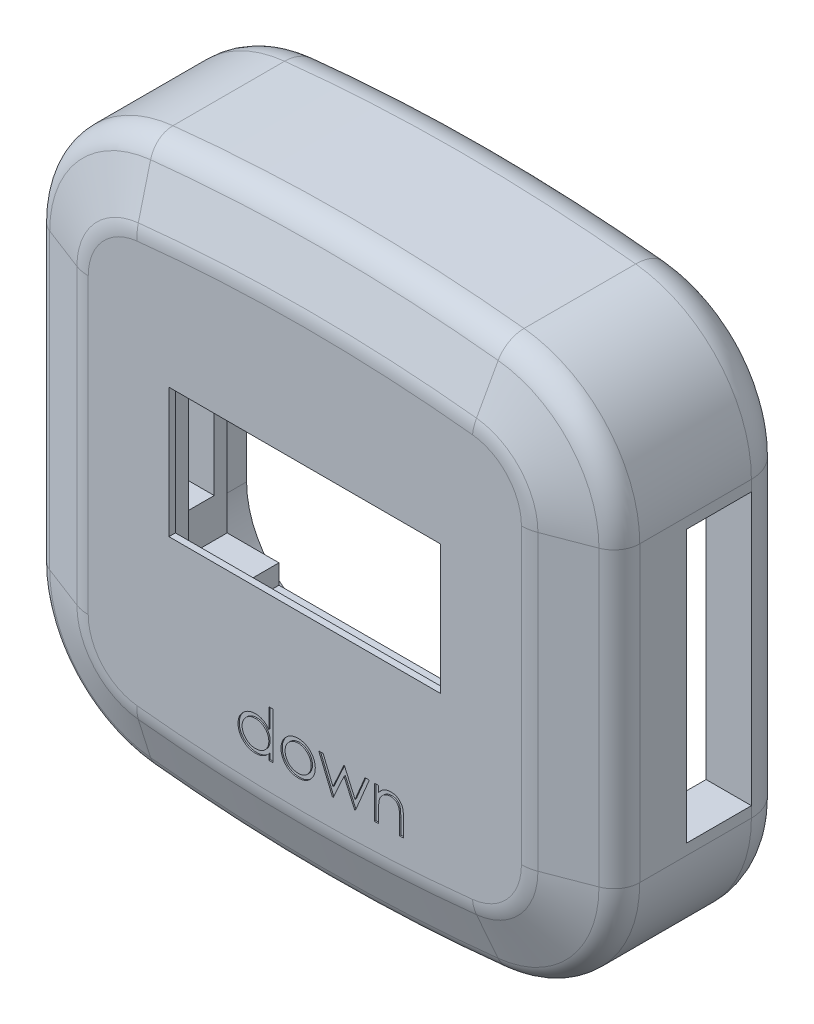
SolidWorks part; units mm, degrees
ref_plane "Plan de face" through (0, 0, 0) normal (0, 0, 1) x (1, 0, 0)
ref_plane "Plan de dessus" through (0, 0, 0) normal (0, 1, 0) x (1, 0, 0)
ref_plane "Plan de droite" through (0, 0, 0) normal (1, 0, 0) x (0, 0, -1)
sketch "Esquisse1" plane through (0, 0, 0) normal (0, 0, 1) x (1, 0, 0)
  line L0 (-2.8778, 47.4702) -> (-2.8778, -48.3378) construction
  line L1 (-25.3778, -11.7674) -> (-2.8778, -11.7674) construction
  line L2 (-25.3778, 10.8998) -> (-25.3778, -11.7674)
  line L3 (-2.8778, -11.7674) -> (19.6222, -11.7674) construction
  line L4 (19.6222, 10.8998) -> (19.6222, -11.7674)
  line L5 (40.0964, -0.4338) -> (-45.852, -0.4338) construction
  line L6 (-16.4411, 20.8431) -> (-16.4411, -0.4338) construction
  line L7 (-16.4411, -0.4338) -> (-16.4411, -21.7107) construction
  arc A0 (10.6854, 20.8431) -> (-16.4411, 20.8431) centre (-2.8778, -105.9963) ccw
  arc A1 (-16.4411, -21.7107) -> (10.6854, -21.7107) centre (-2.8778, 105.1287) ccw
  arc A3 (-16.4411, 20.8431) -> (-25.3778, 10.8998) centre (-15.3778, 10.8998) ccw
  arc A4 (-25.3778, -11.7674) -> (-16.4411, -21.7107) centre (-15.3778, -11.7674) ccw
  arc A5 (10.6854, -21.7107) -> (19.6222, -11.7674) centre (9.6222, -11.7674) ccw
  arc A7 (19.6222, 10.8998) -> (10.6854, 20.8431) centre (9.6222, 10.8998) ccw
  point P5 (-2.8778, -0.4338)
  point P7 (-2.8778, -0.4338)
  point P14 (-2.8778, -22.4338)
  point P17 (-2.8778, 21.5662)
  dimension "D1" = 44
  dimension "D6" = 20
  dimension "D3" = 127.5625
  dimension "D2" = 45
extrude "Boss.-Extru.1" add sketch "Esquisse1" along normal blind 15
fillet "Congé1" radius 3 8 edges at (-2.8778, 21.5662, 0) (-22.8153, 17.5843, 0) (-25.3778, -0.4338, 0) (-22.8153, -18.452, 0) (-2.8778, -22.4338, 0) (17.0597, -18.452, 0) (19.6222, -0.4338, 0) (17.0597, 17.5843, 0)
chamfer "Chanfrein1" distance 2 angle 69 8 edges at (19.6222, -0.4338, 15) (17.0597, -18.452, 15) (-2.8778, -22.4338, 15) (-22.8153, -18.452, 15) (-25.3778, -0.4338, 15) (-22.8153, 17.5843, 15) (-2.8778, 21.5662, 15) (17.0597, 17.5843, 15)
fillet "Congé2" radius 3 8 edges at (-2.8778, -17.2236, 15) (-18.9403, -14.9692, 15) (-20.1677, -0.4338, 15) (-18.9403, 14.1016, 15) (-2.8778, 16.356, 15) (13.1846, 14.1016, 15) (14.412, -0.4338, 15) (13.1846, -14.9692, 15)
fillet "Congé3" radius 2 8 edges at (17.0597, 17.5843, 13) (-2.8778, 21.5662, 13) (-22.8153, 17.5843, 13) (-25.3778, -0.4338, 13) (-22.8153, -18.452, 13) (-2.8778, -22.4338, 13) (17.0597, -18.452, 13) (19.6222, -0.4338, 13)
sketch "Esquisse3" plane through (0, 0, 0) normal (0, 0, -1) x (-1, 0, 0)
  line L0 (2.8778, -19.4338) -> (2.8778, 18.5662) construction
  line L1 (17.8778, -15.4338) -> (-12.1222, -15.4338)
  line L2 (17.8778, -15.4338) -> (17.8778, 14.5662)
  line L3 (17.8778, 14.5662) -> (-12.1222, 14.5662)
  line L4 (-12.1222, -15.4338) -> (-12.1222, 14.5662)
  line L5 (22.3778, -0.4338) -> (-16.6222, -0.4338) construction
  line L6 (22.3778, -11.7674) -> (22.3778, 10.8998) construction
  line L7 (-16.6222, 10.8998) -> (-16.6222, -11.7674) construction
  arc A0 (-10.3664, -18.7277) -> (16.1221, -18.7277) centre (2.8778, 105.1287) ccw construction
  arc A1 (16.1221, 17.8601) -> (-10.3664, 17.8601) centre (2.8778, -105.9963) ccw construction
  point P18 (2.8778, -15.4338)
  point P19 (-12.1222, -0.4338)
  dimension "D1" = 30
sketch "Esquisse7" plane through (0, 0, 15) normal (0, 0, 1) x (1, 0, 0)
  text T0 "down"
extrude "Enlèv. mat.-Extru.4" cut sketch "Esquisse7" against normal blind 0.1
extrude "Enlèv. mat.-Extru.5" cut sketch "Esquisse3" against normal blind 12
sketch "displayFootPrint" plane through (0, 0, 12) normal (0, 0, -1) x (-1, 0, 0)
  line L0 (17.8778, 14.5662) -> (-12.1222, 14.5662) construction
  line L1 (-10.8722, 13.4662) -> (16.6278, 13.4662) construction
  line L2 (-10.8722, 13.4662) -> (-10.8722, -14.3338) construction
  line L3 (-10.8722, -14.3338) -> (16.6278, -14.3338) construction
  line L4 (16.6278, 13.4662) -> (16.6278, -14.3338) construction
  line L5 (17.8778, -15.4338) -> (17.8778, 14.5662) construction
  point P6 (2.8778, 14.5662)
  point P7 (2.8778, 13.4662)
  point P10 (17.8778, -0.4338)
  point P11 (16.6278, -0.4338)
  dimension "D1" = 27.5
  dimension "D2" = 27.8
sketch "Esquisse9" plane through (0, 0, 12) normal (0, 0, -1) x (-1, 0, 0)
  line L0 (-10.8722, 13.4662) -> (16.6278, 13.4662) construction
  line L1 (-10.6222, 9.1662) -> (16.3778, 9.1662)
  line L2 (-10.6222, 9.1662) -> (-10.6222, -10.3338)
  line L3 (-10.6222, -10.3338) -> (16.3778, -10.3338)
  line L4 (16.3778, 9.1662) -> (16.3778, -10.3338)
  point P4 (2.8778, 9.1662)
  point P7 (2.8778, 13.4662)
  dimension "D1" = 27
  dimension "D2" = 19.5
  dimension "D3" = 4.3
sketch "Esquisse10" plane through (0, 0, 15) normal (0, 0, 1) x (1, 0, 0)
  line L0 (10.6222, 9.1662) -> (-16.3778, 9.1662) construction
  line L1 (-13.3778, 6.5662) -> (7.6222, 6.5662)
  line L2 (-13.3778, 6.5662) -> (-13.3778, -3.4338)
  line L3 (-13.3778, -3.4338) -> (7.6222, -3.4338)
  line L4 (7.6222, 6.5662) -> (7.6222, -3.4338)
  line L5 (10.8722, 13.4662) -> (-16.6278, 13.4662) construction
  point P4 (-2.8778, 6.5662)
  point P7 (-2.8778, 9.1662)
  dimension "D1" = 21
  dimension "D2" = 10
  dimension "D3" = 6.9
extrude "Enlèv. mat.-Extru.6" cut sketch "Esquisse10" against normal blind 0.5
extrude "Enlèv. mat.-Extru.7" cut sketch "Esquisse9" against normal up to vertex (2.5 mm away)
sketch "Esquisse11" plane through (0, 0, 14.5) normal (0, 0, -1) x (-1, 0, 0)
  line L0 (2.8778, 6.5662) -> (2.8778, -3.4338) construction
  line L1 (-7.6222, 6.5662) -> (13.3778, 6.5662) construction
  line L2 (13.3778, -3.4338) -> (-7.6222, -3.4338) construction
  line L3 (-7.6222, 1.5662) -> (13.3778, 1.5662) construction
  line L4 (-7.6222, -3.4338) -> (-7.6222, 6.5662) construction
  line L5 (13.3778, 6.5662) -> (13.3778, -3.4338) construction
  point P12 (2.8778, 1.5662)
sketch "Esquisse12" plane through (0, 0, 0) normal (0, 0, -1) x (-1, 0, 0)
  line L0 (2.8778, 14.5662) -> (2.8778, -15.4338) construction
  line L1 (17.8778, 14.5662) -> (-12.1222, 14.5662) construction
  line L2 (-12.1222, -15.4338) -> (17.8778, -15.4338) construction
  line L3 (-12.1222, -0.4338) -> (17.8778, -0.4338) construction
  line L4 (-12.1222, 14.5662) -> (-12.1222, -15.4338) construction
  line L5 (17.8778, -15.4338) -> (17.8778, 14.5662) construction
  point P12 (2.8778, -0.4338)
sketch "Esquisse14" plane through (0, 0, 0) normal (0, 0, -1) x (-1, 0, 0)
  line L1 (-16.6222, 10.8998) -> (-16.6222, -11.7674) construction
  line L2 (22.3778, -11.7674) -> (22.3778, 10.8998) construction
  line L3 (-16.6222, 10.8998) -> (-16.6222, -11.7674)
  line L4 (22.3778, -11.7674) -> (22.3778, 10.8998)
  arc A0 (-10.3664, -18.7277) -> (16.1221, -18.7277) centre (2.8778, 105.1287) ccw construction
  arc A1 (-16.6222, -11.7674) -> (-10.3664, -18.7277) centre (-9.6222, -11.7674) ccw construction
  arc A2 (-10.3664, 17.8601) -> (-16.6222, 10.8998) centre (-9.6222, 10.8998) ccw construction
  arc A3 (16.1221, 17.8601) -> (-10.3664, 17.8601) centre (2.8778, -105.9963) ccw construction
  arc A4 (22.3778, 10.8998) -> (16.1221, 17.8601) centre (15.3778, 10.8998) ccw construction
  arc A5 (16.1221, -18.7277) -> (22.3778, -11.7674) centre (15.3778, -11.7674) ccw construction
  arc A6 (-10.3664, -18.7277) -> (16.1221, -18.7277) centre (2.8778, 105.1287) ccw
  arc A7 (-16.6222, -11.7674) -> (-10.3664, -18.7277) centre (-9.6222, -11.7674) ccw
  arc A8 (-10.3664, 17.8601) -> (-16.6222, 10.8998) centre (-9.6222, 10.8998) ccw
  arc A9 (16.1221, 17.8601) -> (-10.3664, 17.8601) centre (2.8778, -105.9963) ccw
  arc A10 (22.3778, 10.8998) -> (16.1221, 17.8601) centre (15.3778, 10.8998) ccw
  arc A11 (16.1221, -18.7277) -> (22.3778, -11.7674) centre (15.3778, -11.7674) ccw
extrude "Enlèv. mat.-Extru.9" cut sketch "Esquisse14" against normal blind 2
sketch "Esquisse15" plane through (0, 0, 2) normal (0, 0, -1) x (-1, 0, 0)
  line L0 (21.8778, -13.9338) -> (22.3778, -13.9338) construction
  line L1 (21.8778, -13.9338) -> (-16.1222, -13.9338)
  line L2 (21.8778, -13.9338) -> (21.8778, 13.0662)
  line L3 (21.8778, 13.0662) -> (-16.1222, 13.0662)
  line L4 (-16.1222, -13.9338) -> (-16.1222, 13.0662)
  line L5 (22.3778, -11.7674) -> (22.3778, 10.8998) construction
  line L6 (-16.1222, -13.9338) -> (-16.6222, -13.9338) construction
  line L7 (-16.6222, 10.8998) -> (-16.6222, -11.7674) construction
  line L8 (22.3778, -0.4338) -> (-16.6222, -0.4338) construction
  point P12 (21.8778, -0.4338)
  dimension "D1" = 38
  dimension "D2" = 27
extrude "Enlèv. mat.-Extru.10" cut sketch "Esquisse15" against normal blind 7
sketch "Esquisse16" plane through (-21.8778, 0, 0) normal (1, 0, 0) x (0, 0, -1)
  line L0 (-2, -0.4338) -> (-9, -0.4338) construction
  line L1 (-3, 10.0662) -> (-8, 10.0662)
  line L2 (-3, 10.0662) -> (-3, -10.9338)
  line L3 (-3, -10.9338) -> (-8, -10.9338)
  line L4 (-8, 10.0662) -> (-8, -10.9338)
  line L5 (-2, -13.9338) -> (-2, 13.0662) construction
  line L6 (-9, -13.9338) -> (-9, 13.0662) construction
  point P10 (-3, -0.4338)
  dimension "D1" = 21
  dimension "D2" = 5
  dimension "D3" = 1
extrude "Enlèv. mat.-Extru.11" cut sketch "Esquisse16" against normal up to surface and the other way up to surface up to face at (-25.3778, -0.4338, 7.3127) other way up to face at (19.6222, -0.4338, 7.3127)
